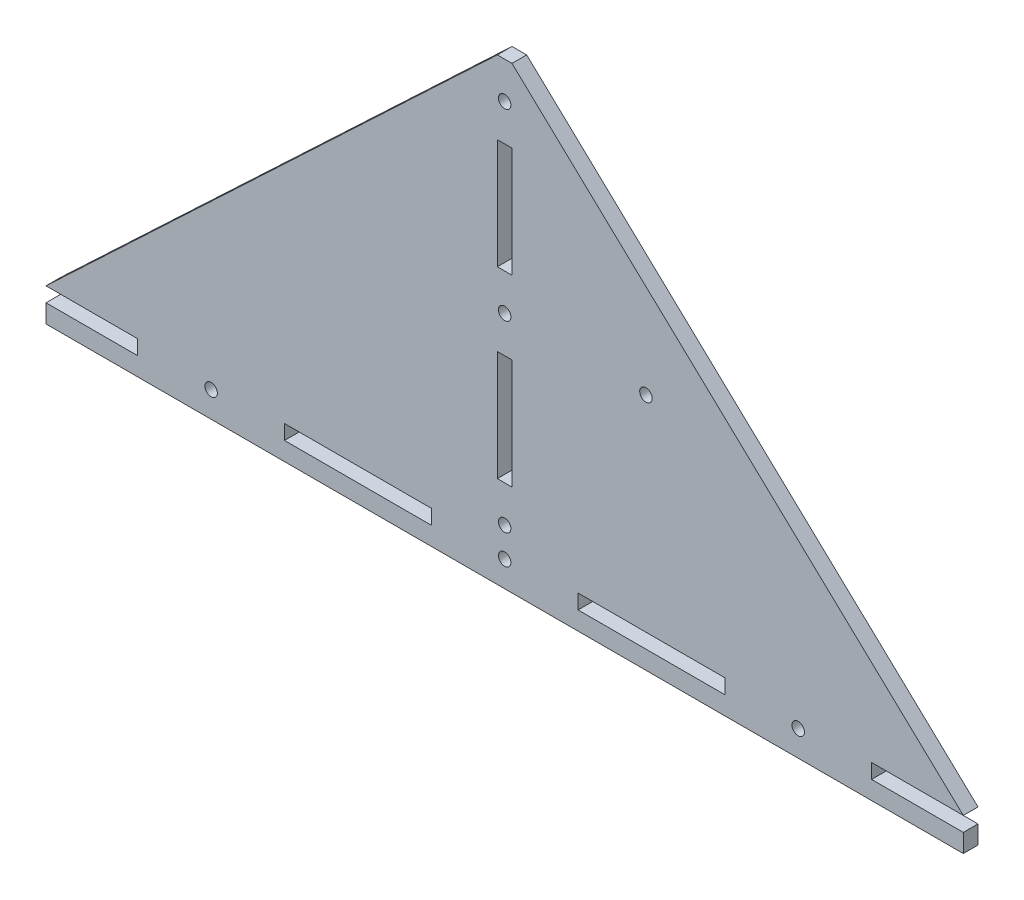
SolidWorks part; units mm, degrees
ref_plane "Plan de face" through (0, 0, 0) normal (0, 0, 1) x (1, 0, 0)
ref_plane "Plan de dessus" through (0, 0, 0) normal (0, 1, 0) x (1, 0, 0)
ref_plane "Plan de droite" through (0, 0, 0) normal (1, 0, 0) x (0, 0, -1)
sketch "Esquisse1" plane through (0, 0, 0) normal (0, 0, 1) x (1, 0, 0)
  line L0 (-8.2566, 32.6907) -> (-4.2566, 32.6907)
  line L1 (-6.2566, 32.6907) -> (-6.2566, -87.3093) construction
  line L2 (-131.2566, -87.3093) -> (118.7434, -87.3093)
  line L3 (-131.2566, -87.3093) -> (-131.2566, -83.3093)
  line L4 (-131.2566, -83.3093) -> (-8.2566, 32.6907)
  line L5 (118.7434, -87.3093) -> (118.7434, -83.3093)
  line L6 (118.7434, -83.3093) -> (-4.2566, 32.6907)
  point P6 (-6.2566, -87.3093)
  dimension "D1" = 4
  dimension "D2" = 120
  dimension "D3" = 250
  dimension "D4" = 4
extrude "Boss.-Extru.1" add sketch "Esquisse1" along normal blind 4
sketch "Esquisse2" plane through (0, 0, 4) normal (0, 0, 1) x (1, 0, 0)
  line L0 (-4.2566, 32.6907) -> (-4.2566, -87.3093) construction
  line L1 (-131.2566, -87.3093) -> (118.7434, -87.3093) construction
  line L2 (-8.2566, 32.6907) -> (-8.2566, -87.3093) construction
  line L4 (-8.2566, 12.6907) -> (-4.2566, 12.6907)
  line L5 (-8.2566, 12.6907) -> (-8.2566, -17.3093)
  line L6 (-8.2566, -17.3093) -> (-4.2566, -17.3093)
  line L7 (-4.2566, 12.6907) -> (-4.2566, -17.3093)
  dimension "D1" = 30
  dimension "D2" = 20
extrude "Enlèv. mat.-Extru.1" cut sketch "Esquisse2" against normal blind 4
pattern_linear "Répétition linéaire1" count 2 spacing 50 along (0, -1, 0) of "Enlèv. mat.-Extru.1"
sketch "Esquisse3" plane through (0, 0, 4) normal (0, 0, 1) x (1, 0, 0)
  line L0 (-131.2566, -87.3093) -> (118.7434, -87.3093) construction
  line L1 (-131.2566, -83.3093) -> (-106.2566, -83.3093)
  line L2 (-131.2566, -83.3093) -> (-131.2566, -87.3093)
  line L3 (-131.2566, -87.3093) -> (-106.2566, -87.3093)
  line L4 (-106.2566, -83.3093) -> (-106.2566, -87.3093)
  line L5 (13.7434, -87.3093) -> (13.7434, -83.3093)
  line L6 (-66.2566, -87.3093) -> (-26.2566, -87.3093)
  line L7 (-66.2566, -87.3093) -> (-66.2566, -83.3093)
  line L8 (-66.2566, -83.3093) -> (-26.2566, -83.3093)
  line L9 (-26.2566, -87.3093) -> (-26.2566, -83.3093)
  line L10 (13.7434, -87.3093) -> (53.7434, -87.3093)
  line L11 (53.7434, -87.3093) -> (53.7434, -83.3093)
  line L12 (13.7434, -83.3093) -> (53.7434, -83.3093)
  line L13 (93.7434, -87.3093) -> (93.7434, -83.3093)
  line L14 (93.7434, -87.3093) -> (133.7434, -87.3093)
  line L15 (133.7434, -87.3093) -> (133.7434, -83.3093)
  line L16 (93.7434, -83.3093) -> (133.7434, -83.3093)
  dimension "D1" = 25
  dimension "D2" = 40
  dimension "D3" = 40
  dimension "D4" = 3
extrude "Enlèv. mat.-Extru.2" cut sketch "Esquisse3" against normal blind 4
sketch "Esquisse4" plane through (0, 0, 4) normal (0, 0, 1) x (1, 0, 0)
  line L0 (-6.2566, -17.3093) -> (-6.2566, -37.3093) construction
  line L1 (-8.2566, -17.3093) -> (-4.2566, -17.3093) construction
  line L2 (-4.2566, -37.3093) -> (-8.2566, -37.3093) construction
  line L3 (-106.2566, -85.3093) -> (-66.2566, -85.3093) construction
  line L4 (-106.2566, -87.3093) -> (-106.2566, -83.3093) construction
  line L5 (-66.2566, -83.3093) -> (-66.2566, -87.3093) construction
  line L6 (-66.2566, -85.3093) -> (-26.2566, -85.3093) construction
  line L7 (-26.2566, -87.3093) -> (-26.2566, -83.3093) construction
  line L8 (-26.2566, -85.3093) -> (13.7434, -85.3093) construction
  line L9 (13.7434, -83.3093) -> (13.7434, -87.3093) construction
  line L10 (13.7434, -85.3093) -> (53.7434, -85.3093) construction
  line L11 (53.7434, -87.3093) -> (53.7434, -83.3093) construction
  line L12 (53.7434, -85.3093) -> (93.7434, -85.3093) construction
  line L13 (93.7434, -83.3093) -> (93.7434, -87.3093) construction
  line L14 (-6.2566, -67.3093) -> (-6.2566, -87.3093) construction
  line L15 (-8.2566, -67.3093) -> (-4.2566, -67.3093) construction
  line L16 (-26.2566, -87.3093) -> (13.7434, -87.3093) construction
  line L17 (-6.2566, 12.6907) -> (-6.2566, 32.6907) construction
  line L18 (-4.2566, 12.6907) -> (-8.2566, 12.6907) construction
  line L19 (-6.2566, 32.6907) -> (-6.2566, 22.6907) construction
  line L20 (-6.2566, -17.3093) -> (-6.2566, -27.3093) construction
  line L21 (-6.2566, -67.3093) -> (-6.2566, -77.3093) construction
  line L22 (-106.2566, -85.3093) -> (-86.2566, -85.3093) construction
  line L23 (53.7434, -85.3093) -> (73.7434, -85.3093) construction
  line L24 (13.7434, -85.3093) -> (-6.2566, -85.3093) construction
hole_wizard "Dégagement M31" positions "Esquisse7" profile "Esquisse8" hole size "M3" standard "ISO" end condition through all
sketch "Esquisse7" plane through (0, 0, 4) normal (0, 0, 1) x (1, 0, 0)
  point P0 (-6.2566, 22.6907)
  point P3 (-6.2566, -27.3093)
  point P6 (-6.2566, -77.3093)
  point P9 (-6.2566, -85.3093)
  point P12 (-86.2566, -85.3093)
  point P15 (73.7434, -85.3093)
sketch "Esquisse8" plane through (-6.2566, 22.6907, 4) normal (1, 0, 0) x (0, -1, 0)
  line L0 (0, 0) -> (0, 4)
  line L1 (0, 4) -> (1.7, 4)
  line L2 (1.7, 4) -> (1.7, 0)
  line L5 (1.7, 0) -> (0, 0)
  line L11 (0, -6.35) -> (0, 107.95) construction
  dimension "Diamètre du perçage jusqu'au prochain" = 3.4
  dimension "Profondeur du perçage jusqu'au prochain" = 4
sketch "Esquisse9" plane through (0, -87.3093, 0) normal (0, -1, 0) x (1, 0, 0)
  line L0 (-6.2566, 4) -> (-131.2566, 4) construction
  line L2 (-131.2566, 4) -> (118.7434, 4)
  line L3 (-131.2566, 4) -> (-131.2566, 0)
  line L4 (-131.2566, 0) -> (118.7434, 0)
  line L5 (118.7434, 4) -> (118.7434, 0)
  dimension "D1" = 125
  dimension "D2" = 250
extrude "Boss.-Extru.2" add sketch "Esquisse9" along normal blind 5
extrude "Enlèv. mat.-Extru.3" cut sketch "Esquisse10" against normal blind 10
sketch "Esquisse10" plane through (-276.2566, 4.3243, 4) normal (0, 0, 1) x (1, 0, 0)
  circle A0 centre (308.5, -31.6336) radius 1.7
